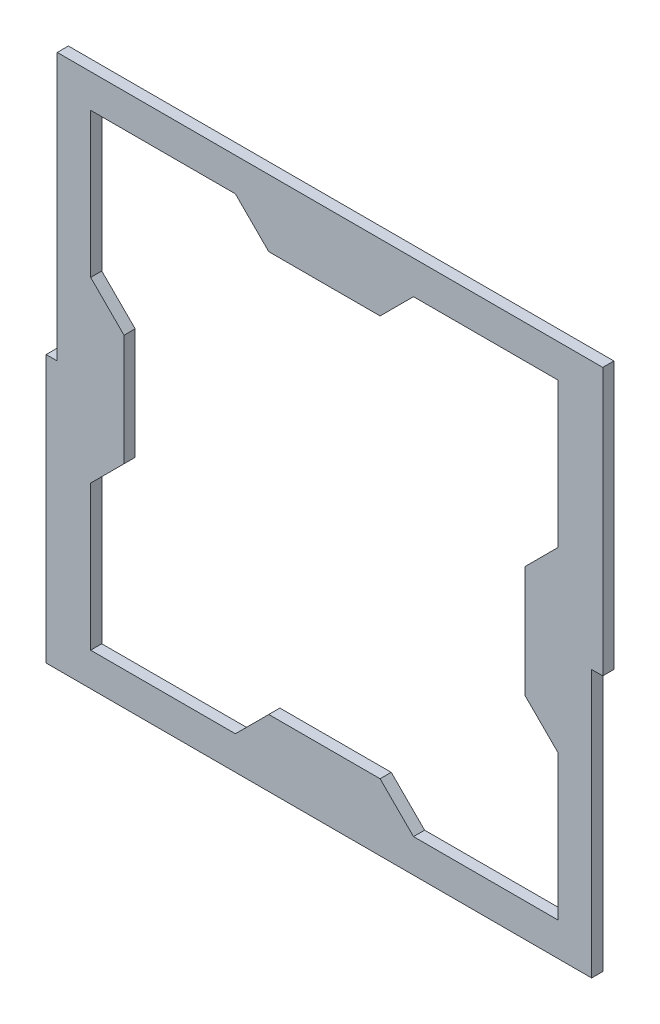
SolidWorks part; units mm, degrees
ref_plane "Front Plane" through (0, 0, 0) normal (0, 0, 1) x (1, 0, 0)
ref_plane "Top Plane" through (0, 0, 0) normal (0, 1, 0) x (1, 0, 0)
ref_plane "Right Plane" through (0, 0, 0) normal (1, 0, 0) x (0, 0, -1)
sketch "Sketch1" plane through (0, 0, 0) normal (0, 0, 1) x (1, 0, 0)
  line L0 (-25.4, 66.675) -> (-15.875, 57.15)
  line L1 (76.2, -76.2) -> (-76.2, -76.2)
  line L2 (76.2, -76.2) -> (76.2, 76.2)
  line L3 (76.2, 76.2) -> (-76.2, 76.2)
  line L4 (-76.2, -76.2) -> (-76.2, 76.2)
  line L5 (76.2, -76.2) -> (-76.2, 76.2) construction
  line L6 (76.2, 76.2) -> (-76.2, -76.2) construction
  line L7 (66.675, -66.675) -> (-66.675, -66.675)
  line L8 (66.675, -66.675) -> (66.675, 66.675)
  line L9 (66.675, 66.675) -> (-66.675, 66.675)
  line L10 (-66.675, -66.675) -> (-66.675, 66.675)
  line L11 (66.675, -66.675) -> (-66.675, 66.675) construction
  line L12 (66.675, 66.675) -> (-66.675, -66.675) construction
  line L13 (57.15, -57.15) -> (-57.15, -57.15)
  line L14 (57.15, -57.15) -> (57.15, 57.15)
  line L15 (57.15, 57.15) -> (-57.15, 57.15)
  line L16 (-57.15, -57.15) -> (-57.15, 57.15)
  line L17 (57.15, -57.15) -> (-57.15, 57.15) construction
  line L18 (57.15, 57.15) -> (-57.15, -57.15) construction
  line L19 (15.875, 57.15) -> (25.4, 66.675)
  line L20 (57.15, -15.875) -> (66.675, -25.4)
  line L21 (66.675, 25.4) -> (57.15, 15.875)
  line L22 (-15.875, -57.15) -> (-25.4, -66.675)
  line L23 (25.4, -66.675) -> (15.875, -57.15)
  line L24 (-57.15, 15.875) -> (-66.675, 25.4)
  line L25 (-66.675, -25.4) -> (-57.15, -15.875)
  point P0 (0, 0)
  point P6 (0, 0)
  point P11 (0, 0)
  point P35 (0, 0)
  dimension "D1" = 152.4
  dimension "D2" = 152.4
  dimension "D3" = 9.525
  dimension "D4" = 9.525
  dimension "D5" = 31.75
  dimension "D6" = 15.875
  dimension "D7" = 4
extrude "Boss-Extrude1" add sketch "Sketch1" along normal blind 3.175 contours L4 L1 L2 L3 L7 L10 L9 L8 | L15 L19 L9 L0 | L8 L21 L14 L20 | L7 L23 L13 L22 | L10 L25 L16 L24
sketch "Sketch2" plane through (0, 0, 3.175) normal (0, 0, 1) x (1, 0, 0)
  line L6 (76.2, -76.2) -> (79.375, -76.2)
  line L7 (76.2, -76.2) -> (76.2, 76.2)
  line L8 (76.2, 76.2) -> (79.375, 76.2)
  line L9 (79.375, -76.2) -> (79.375, 76.2)
  dimension "D3" = 3.175
extrude "Boss-Extrude4" add sketch "Sketch2" against normal blind 3.175 contours L9 L8 L7 L6
sketch "Sketch3" plane through (0, 0, 3.175) normal (0, 0, 1) x (1, 0, 0)
  line L1 (79.375, 76.2) -> (76.2, 76.2)
  line L2 (79.375, 76.2) -> (79.375, 0)
  line L3 (79.375, 0) -> (76.2, 0)
  line L4 (76.2, 76.2) -> (76.2, 0)
  line L5 (-76.2, -76.2) -> (-79.375, -76.2)
  line L6 (-76.2, -76.2) -> (-76.2, 0)
  line L7 (-76.2, 0) -> (-79.375, 0)
  line L8 (-79.375, -76.2) -> (-79.375, 0)
  dimension "D1" = 3.175
  dimension "D2" = 3.175
  dimension "D3" = 76.2
  dimension "D4" = 76.2
extrude "Boss-Extrude5" add sketch "Sketch3" against normal blind 3.175
sketch "Sketch4" plane through (0, 0, 3.175) normal (0, 0, 1) x (1, 0, 0)
  line L1 (79.375, 0) -> (76.2, 0)
  line L2 (79.375, 0) -> (79.375, -76.2)
  line L3 (79.375, -76.2) -> (76.2, -76.2)
  line L4 (76.2, 0) -> (76.2, -76.2)
  dimension "D1" = 3.175
  dimension "D2" = 76.2
extrude "Cut-Extrude1" cut sketch "Sketch4" against normal blind 3.175
